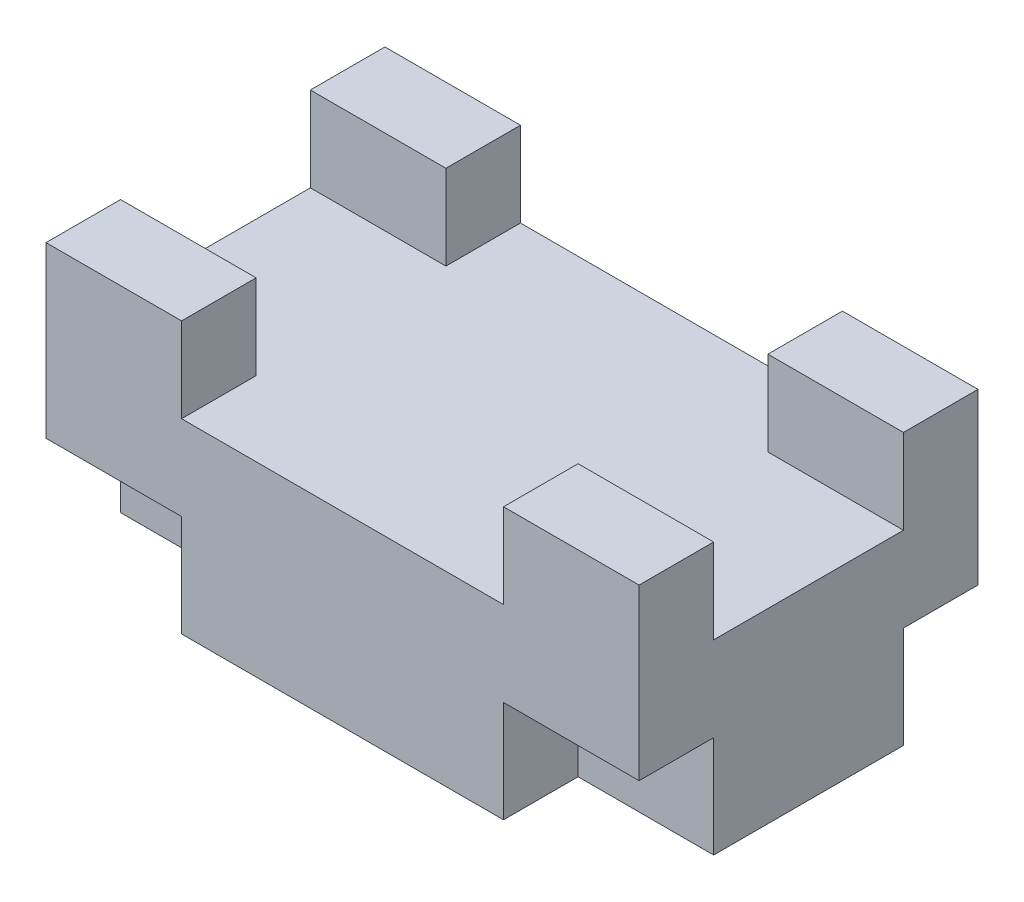
SolidWorks part; units mm, degrees
ref_plane "Front Plane" through (0, 0, 0) normal (0, 0, 1) x (1, 0, 0)
ref_plane "Top Plane" through (0, 0, 0) normal (0, 1, 0) x (1, 0, 0)
ref_plane "Right Plane" through (0, 0, 0) normal (1, 0, 0) x (0, 0, -1)
sketch "Sketch1" plane through (0, 0, 0) normal (0, 1, 0) x (1, 0, 0)
  line L1 (-87.5, -50) -> (87.5, -50)
  line L2 (-87.5, -50) -> (-87.5, 50)
  line L3 (-87.5, 50) -> (87.5, 50)
  line L4 (87.5, -50) -> (87.5, 50)
  line L5 (-87.5, -50) -> (87.5, 50) construction
  line L6 (-87.5, 50) -> (87.5, -50) construction
  point P0 (0, 0)
  dimension "D1" = 175
  dimension "D2" = 100
extrude "Boss-Extrude1" add sketch "Sketch1" along normal blind 80
sketch "Sketch2" plane through (0, 0, 50) normal (0, 0, 1) x (1, 0, 0)
  line L0 (-87.5, 80) -> (87.5, 80) construction
  line L1 (-47.5, 80) -> (47.5, 80)
  line L2 (-47.5, 80) -> (-47.5, 55)
  line L3 (-47.5, 55) -> (47.5, 55)
  line L4 (47.5, 80) -> (47.5, 55)
  line L5 (-87.5, 80) -> (-87.5, 0) construction
  line L6 (87.5, 80) -> (87.5, 0) construction
  dimension "D1" = 40
  dimension "D2" = 40
  dimension "D3" = 25
extrude "Cut-Extrude1" cut sketch "Sketch2" against normal through all
sketch "Sketch3" plane through (87.5, 0, 0) normal (1, 0, 0) x (0, 0, -1)
  line L0 (-50, 80) -> (50, 80) construction
  line L1 (-28, 80) -> (28, 80)
  line L2 (-28, 80) -> (-28, 55)
  line L3 (-28, 55) -> (28, 55)
  line L4 (28, 80) -> (28, 55)
  line L5 (-50, 80) -> (-50, 0) construction
  line L6 (50, 80) -> (50, 0) construction
  dimension "D1" = 25
  dimension "D2" = 22
  dimension "D3" = 22
extrude "Cut-Extrude2" cut sketch "Sketch3" against normal through all
sketch "Sketch4" plane through (0, 0, 50) normal (0, 0, 1) x (1, 0, 0)
  line L0 (-87.5, 80) -> (-87.5, 0) construction
  line L1 (-87.5, 30) -> (-47.5, 30)
  line L2 (-87.5, 30) -> (-87.5, 0)
  line L3 (-87.5, 0) -> (-47.5, 0)
  line L4 (-47.5, 30) -> (-47.5, 0)
  line L5 (-87.5, 0) -> (87.5, 0) construction
  line L6 (0, 0) -> (0, 28.3915) construction
  line L7 (-47.5, 80) -> (-47.5, 55) construction
  line L8 (87.5, 0) -> (47.5, 0)
  line L9 (47.5, 30) -> (47.5, 0)
  line L10 (87.5, 30) -> (47.5, 30)
  line L11 (87.5, 30) -> (87.5, 0)
  dimension "D1" = 30
extrude "Cut-Extrude3" cut sketch "Sketch4" against normal blind 22
ref_plane "Plane1" through (0, 0, 0) normal (0, 0, 1) x (1, 0, 0)
mirror "Mirror1" about plane through (0, 0, 0) normal (0, 0, 1) of "Cut-Extrude3"
